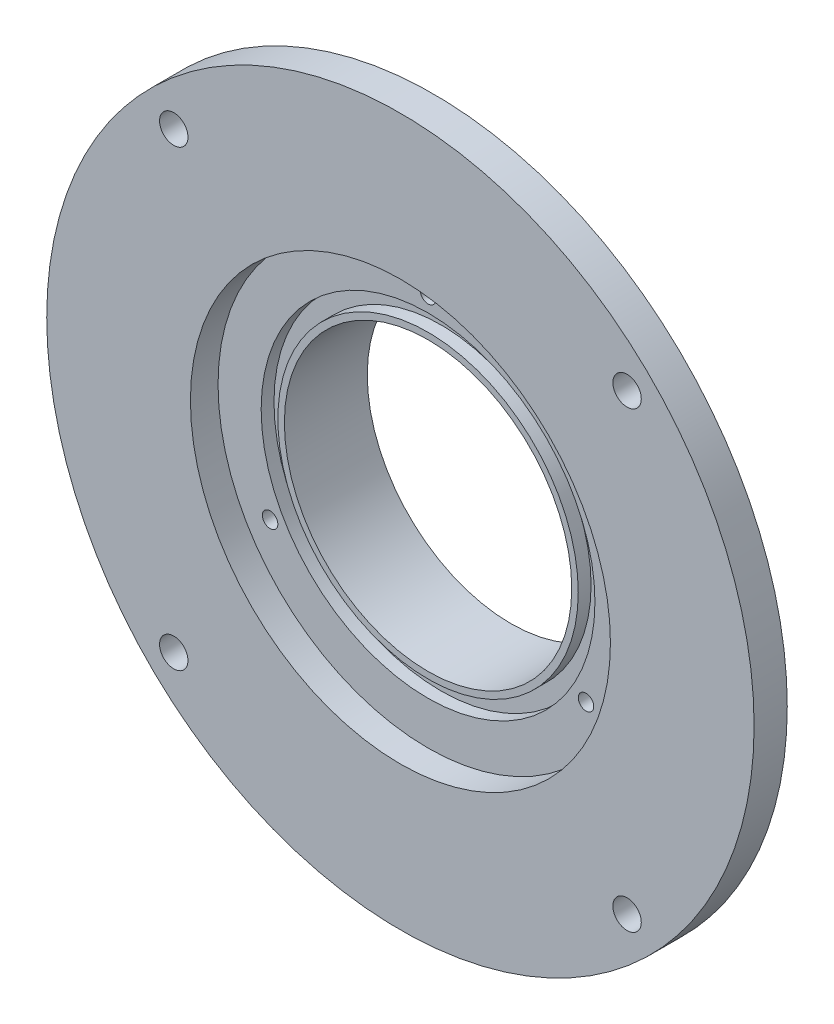
SolidWorks part; units mm, degrees
other "DetailItem1"
ref_plane "Front Plane" through (0, 0, 0) normal (0, 0, 1) x (1, 0, 0)
ref_plane "Top Plane" through (0, 0, 0) normal (0, 1, 0) x (1, 0, 0)
ref_plane "Right Plane" through (0, 0, 0) normal (1, 0, 0) x (0, 0, -1)
sketch "Sketch1" plane through (0, 0, 0) normal (0, 0, 1) x (1, 0, 0)
  circle A0 centre (0, 0) radius 40.64
  dimension "D1" = 81.28
extrude "Extrude1" add sketch "Sketch1" along normal blind 3.81
hole_wizard "#4 Clearance Hole1" positions "Sketch3" profile "Sketch2" hole size "#4" standard "ANSI Inch" end condition through all
sketch "Sketch3" plane through (0, 0, 3.81) normal (0, 0, 1) x (1, 0, 0)
  line L0 (0, 0) -> (0, 33.0714) construction
  line L1 (0, 0) -> (0, -33.2166) construction
  line L2 (0, 0) -> (36.629, 0) construction
  line L3 (0, 0) -> (-36.7743, 0) construction
  point P0 (26.0427, 26.0427)
  point P18 (26.0427, -26.0427)
  point P21 (-26.0423, 26.0432)
  point P27 (-26.0425, -26.043)
  dimension "D1" = 36.83
  dimension "D4" = 36.83
  dimension "D5" = 36.83
  dimension "D8" = 36.83
  dimension "D2" = 45
  dimension "D3" = 45
  dimension "D6" = 45.001
  dimension "D7" = 45.001
sketch "Sketch2" plane through (26.0427, 26.0427, 3.81) normal (1, 0, 0) x (0, -1, 0)
  line L0 (0, 0) -> (0, 3.81)
  line L1 (0, 3.81) -> (1.6319, 3.81)
  line L2 (1.6319, 3.81) -> (1.6319, 0)
  line L5 (1.6319, 0) -> (0, 0)
  line L11 (0, -6.35) -> (0, 107.95) construction
  dimension "Thru Hole Dia." = 3.2639
  dimension "Thru Hole Depth" = 3.81
sketch "Sketch4" [suppressed] plane through (0, 0, 3.81) normal (0, 0, 1) x (1, 0, 0)
  circle A0 centre (-26.0423, 26.0432) radius 2.794
  circle A1 centre (26.0427, 26.0427) radius 2.794
  circle A2 centre (-26.0425, -26.043) radius 2.794
  circle A3 centre (26.0427, -26.0427) radius 2.794
extrude "Cut-Extrude1" [suppressed] cut sketch "Sketch4" against normal blind 3.302
sketch "Sketch6" plane through (0, 0, 0) normal (0, 0, -1) x (-1, 0, 0)
  circle A0 centre (0, 0) radius 27.94
  dimension "D1" = 55.88
extrude "Extrude2" add sketch "Sketch6" along normal blind 8.89
sketch "Sketch5" plane through (0, 0, 3.81) normal (0, 0, 1) x (1, 0, 0)
  circle A0 centre (0, 0) radius 16.51
  dimension "D1" = 33.02
extrude "Cut-Extrude2" cut sketch "Sketch5" against normal through all
chamfer "Chamfer1" [suppressed] distance 0.508 angle 45
sketch "Sketch14" plane through (0, 0, 3.81) normal (0, 0, 1) x (1, 0, 0)
  circle A0 centre (0, 0) radius 24.13
  dimension "D1" = 48.26
extrude "Cut-Extrude3" cut sketch "Sketch14" against normal blind 3.175
hole_wizard "#2-56 Tapped Hole1" positions "Sketch15" profile "Sketch16" tap size "#2-56" standard "ANSI Inch"
sketch "Sketch15" plane through (0, 0, 0.635) normal (0, 0, 1) x (1, 0, 0)
  point P0 (0, 20.955)
  dimension "D1" = 20.955
sketch "Sketch16" plane through (0, 20.955, 0.635) normal (1, 0, 0) x (0, -1, 0)
  line L0 (0, 0) -> (0, 4.9538)
  line L1 (0, 4.9538) -> (0.889, 4.4196)
  line L2 (0.889, 4.4196) -> (0.889, 0)
  line L5 (0.889, 0) -> (0, 0)
  line L10 (0, 4.9538) -> (-0.889, 4.4196) construction
  line L11 (0, -6.35) -> (0, 107.95) construction
  dimension "Tap Drill Dia." = 1.778
  dimension "Tap Drill Depth" = 4.4196
  dimension "Drill Angle" = 118
cosmetic thread "Hole Thread1" parameters "D1"=3.048, "D2"=2.1844
pattern_circular "CirPattern1" count 3 over 360 about axis through (0, 0, 0) along (0, 0, 1) of "#2-56 Tapped Hole1"
sketch "Sketch13" plane through (0, 0, 0.635) normal (0, 0, 1) x (1, 0, 0)
  circle A0 centre (0, 0) radius 17.2593
  circle A1 centre (0, 0) radius 19.177
  dimension "D1" = 34.5186
  dimension "D2" = 38.354
extrude "Cut-Extrude4" cut sketch "Sketch13" against normal blind 1.4732
equation "\"D1@Sketch3\"=\"D5@Sketch3\""
equation "\"D8@Sketch3\"=\"D1@Sketch3\""
equation "\"D4@Sketch3\"=\"D1@Sketch3\""
